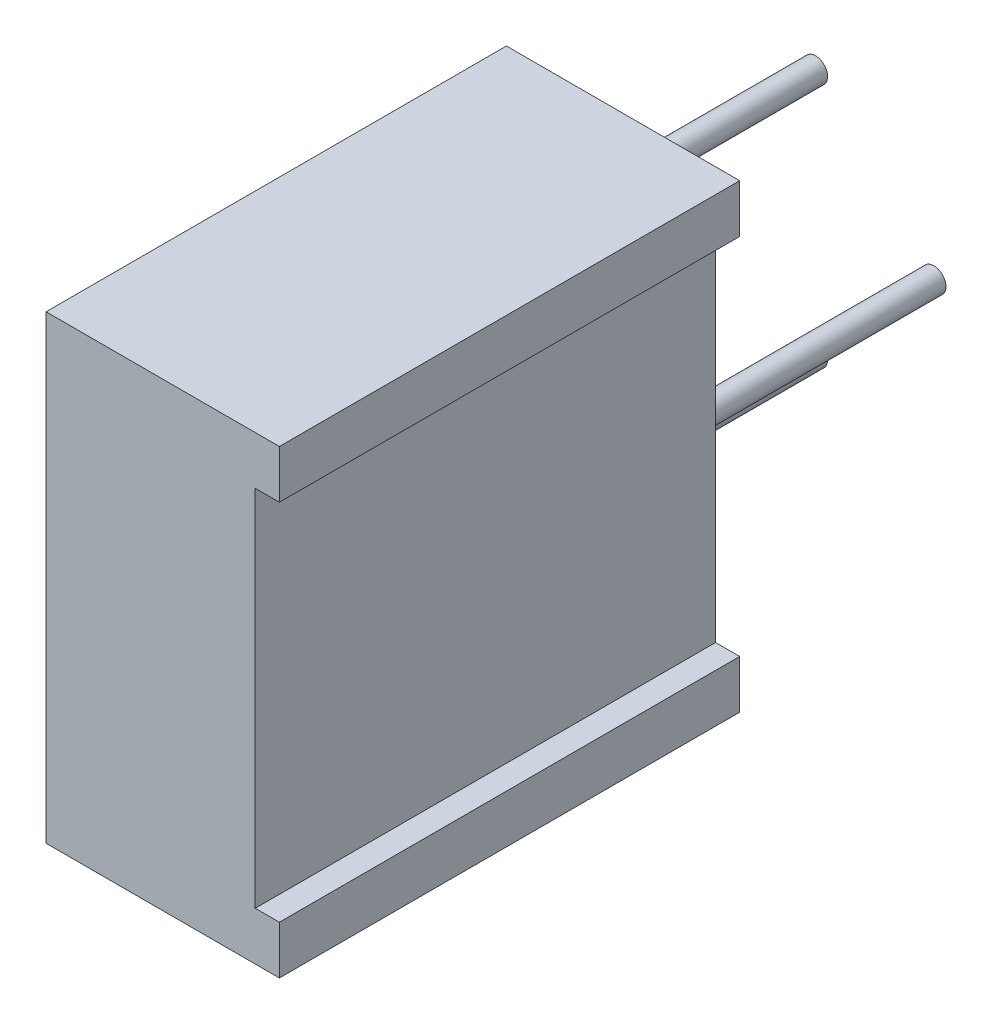
SolidWorks part; units mm, degrees
ref_plane "Front Plane" through (0, 0, 0) normal (0, 0, 1) x (1, 0, 0)
ref_plane "Top Plane" through (0, 0, 0) normal (0, 1, 0) x (1, 0, 0)
ref_plane "Right Plane" through (0, 0, 0) normal (1, 0, 0) x (0, 0, -1)
sketch "Sketch1" plane through (0, 0, 0) normal (1, 0, 0) x (0, 0, 1)
  line L0 (0, 0) -> (9.53, 0)
  line L1 (0, 0) -> (0, 9.53)
  line L2 (9.53, 9.53) -> (0, 9.53)
  line L3 (9.53, 9.53) -> (9.53, 0)
  dimension "D1" = 9.53
extrude "Basic Shape" add sketch "Sketch1" along normal blind 4.83
sketch "Sketch3" plane through (0, 0, 0) normal (1, 0, 0) x (0, 1, 0)
  line L0 (-9.53, 9.53) -> (0, 9.53) construction
  line L1 (0, 0) -> (0, 9.53) construction
  circle A0 centre (-4.765, 4.765) radius 2
  point P2 (-4.765, 9.53)
  point P3 (0, 4.765)
  dimension "D1" = 4
extrude "Adjuster" cut sketch "Sketch3" along normal blind 0.1
sketch "Sketch4" plane through (0.1, 0, 0) normal (-1, 0, 0) x (0, -1, 0)
  line L0 (3.7492, 6.4879) -> (6.4879, 3.7492)
  line L1 (3.0421, 5.7808) -> (5.7808, 3.0421)
  line L2 (5.1186, 5.1186) -> (4.4114, 4.4114) construction
  line L3 (9.53, 9.53) -> (0, 9.53) construction
  circle A0 centre (4.765, 4.765) radius 2 construction
  circle A1 centre (4.765, 4.765) radius 2 construction
  arc A3 (3.7492, 6.4879) -> (3.0421, 5.7808) centre (4.765, 4.765) ccw
  arc A4 (5.7808, 3.0421) -> (6.4879, 3.7492) centre (4.765, 4.765) ccw
  point P6 (4.765, 4.765)
  dimension "D2" = 45
  dimension "D1" = 1
extrude "Adjuster Slot" cut sketch "Sketch4" against normal blind 1
sketch "Sketch5" plane through (0, -19.06, 0) normal (0, 0, -1) x (0, -1, 0)
  line L0 (-9.53, 0) -> (-19.06, 0) construction
  line L1 (-14.295, -1.1) -> (-14.295, -0.1) construction
  circle A0 centre (-16.835, -1.4) radius 0.25
  circle A1 centre (-14.295, -3.85) radius 0.25
  circle A2 centre (-11.755, -1.4) radius 0.25
  point P8 (-14.295, 0)
  dimension "D4" = 0.5
  dimension "D1" = 1.4
  dimension "D2" = 2.45
  dimension "D3" = 2.54
  dimension "D5" = 2.54
extrude "Pins" add sketch "Sketch5" along normal blind 5
sketch "Sketch6" plane through (0, 0, 9.53) normal (0, 0, 1) x (1, 0, 0)
  line L0 (4.83, 0) -> (4.83, -9.53) construction
  line L3 (4.33, -8.53) -> (4.33, -1)
  line L4 (4.83, -1) -> (0, -1)
  line L5 (4.33, -1) -> (4.83, -1)
  line L6 (4.83, -8.53) -> (0, -8.53)
  line L7 (4.33, -8.53) -> (4.83, -8.53)
  line L9 (4.83, -8.53) -> (4.83, -1)
  dimension "D1" = 0.5
  dimension "D2" = 1
  dimension "D3" = 1
extrude "Rear Relief" cut sketch "Sketch6" against normal through all
ref_plane "Board Plane" through (0, 0, -1) normal (0, 0, 1) x (1, 0, 0)
sketch "Component_Outline" plane through (0, 0, -1) normal (0, 0, 1) x (1, 0, 0)
  line L0 (0, 0) -> (0, -9.53)
  line L1 (0, -9.53) -> (4.83, -9.53)
  line L2 (4.83, -9.53) -> (4.83, -8.53)
  line L3 (4.83, -8.53) -> (4.33, -8.53)
  line L4 (4.33, -8.53) -> (4.33, -1)
  line L5 (4.33, -1) -> (4.83, -1)
  line L6 (4.83, -1) -> (4.83, 0)
  line L7 (4.83, 0) -> (0, 0)
